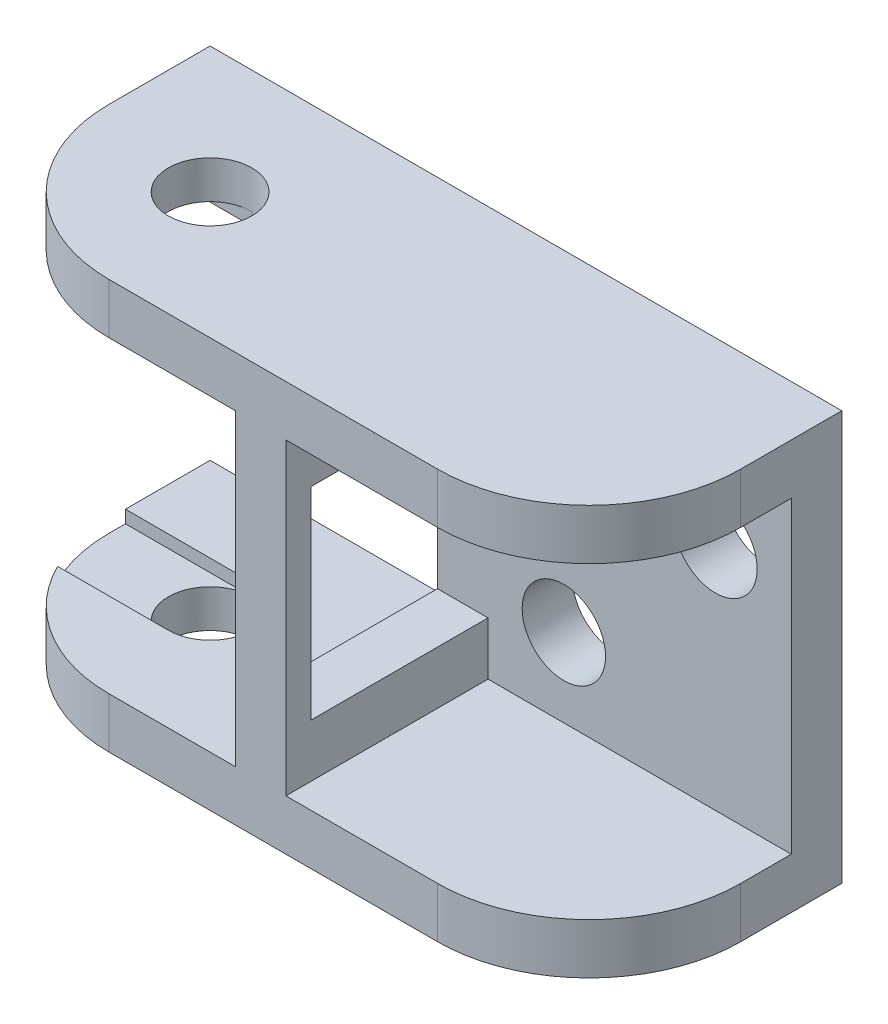
SolidWorks part; units mm, degrees
material "Сталь 45 ГОСТ 1050-2013"
ref_plane "Спереди" through (0, 0, 0) normal (0, 0, 1) x (1, 0, 0)
ref_plane "Сверху" through (0, 0, 0) normal (0, 1, 0) x (1, 0, 0)
ref_plane "Справа" through (0, 0, 0) normal (1, 0, 0) x (0, 0, -1)
sketch "Эскиз2" plane through (0, 0, 0) normal (0, 0, 1) x (1, 0, 0)
  line L0 (0, 0) -> (0, 2)
  line L1 (0, 2) -> (13, 2)
  line L2 (13, 2) -> (13, -0.1)
  line L3 (13, -0.1) -> (24, -0.1)
  line L4 (24, -0.1) -> (24, -2.1)
  line L5 (24, -2.1) -> (11, -2.1)
  line L6 (11, -2.1) -> (11, 0)
  line L7 (11, 0) -> (0, 0)
  dimension "D1" = 2
  dimension "D2" = 24
  dimension "D3" = 2
  dimension "D4" = 11
  dimension "D5" = 0.1
  dimension "D6" = 2
extrude "Бобышка-Вытянуть2" add sketch "Эскиз2" along normal blind 10
sketch "Эскиз3" plane through (0, -0.1, 0) normal (0, 1, 0) x (1, 0, 0)
  line L0 (0, -10) -> (0, 0) construction
  line L1 (24, -10) -> (24, 0) construction
  circle A0 centre (6, -5) radius 1.5 construction
  circle A1 centre (18.1, -5) radius 1.5
  point P5 (0, -5)
  dimension "D1" = 3
  dimension "D2" = 5.9
  dimension "D3" = 6
extrude "Бобышка-Вытянуть3" add sketch "Эскиз3" along normal blind 1.5
sketch "Эскиз5" plane through (0, 0, 0) normal (0, -1, 0) x (1, 0, 0)
  line L0 (0, 10) -> (0, 0) construction
  circle A0 centre (5, 5) radius 1.65
  point P2 (0, 5)
  dimension "D1" = 3.3
  dimension "D2" = 5
extrude "Вырез-Вытянуть2" cut sketch "Эскиз5" against normal through all
fillet "Скругление1" radius 6 2 edges at (24, -1.1, 10) (0, 1, 10)
sketch "Эскиз6" plane through (0, -2.1, 0) normal (0, -1, 0) x (-1, 0, 0)
  line L1 (-11, 0) -> (-21, 0)
  line L2 (-11, 0) -> (-11, -1)
  line L3 (-11, -1) -> (-21, -1)
  line L4 (-21, 0) -> (-21, -1)
  line L5 (-11, 0) -> (-21, -1) construction
  line L6 (-11, -1) -> (-21, 0) construction
  line L7 (-11, -9) -> (-16, -9)
  line L8 (-11, -9) -> (-11, -10)
  line L9 (-11, -10) -> (-16, -10)
  line L10 (-16, -9) -> (-16, -10)
  line L11 (-11, -9) -> (-16, -10) construction
  line L12 (-11, -10) -> (-16, -9) construction
  point P0 (-16, -0.5)
  point P5 (-13.5, -9.5)
  dimension "D1" = 1
  dimension "D2" = 10
  dimension "D3" = 5
extrude "Бобышка-Вытянуть4" add sketch "Эскиз6" along normal blind 4
sketch "Эскиз7" plane through (0, 0, 0) normal (0, -1, 0) x (1, 0, 0)
  line L1 (-0.6896, 3.35) -> (5, 3.35)
  line L2 (-0.6896, 3.35) -> (-0.6896, 6.65)
  line L3 (-0.6896, 6.65) -> (5, 6.65)
  line L4 (5, 3.35) -> (5, 6.65)
  line L5 (-0.6896, 3.35) -> (5, 6.65) construction
  line L6 (-0.6896, 6.65) -> (5, 3.35) construction
  circle A0 centre (5, 5) radius 1.65 construction
  point P0 (2.1552, 5)
extrude "Вырез-Вытянуть3" cut sketch "Эскиз7" against normal blind 0.5
mirror "Зеркальное отражение1" about plane through (0, -6.1, 0) normal (0, 1, 0) of bodies 111 109
sketch "Эскиз8" plane through (0, 0, 10) normal (0, 0, 1) x (1, 0, 0)
  line L0 (13, -14.2) -> (6, -14.2) construction
  line L1 (27.1965, -14.2) -> (13, -14.2)
  line L2 (27.1965, -14.2) -> (27.1965, 2)
  line L3 (27.1965, 2) -> (13, 2)
  line L4 (13, -14.2) -> (13, 2)
  line L5 (27.1965, -14.2) -> (13, 2) construction
  line L6 (27.1965, 2) -> (13, -14.2) construction
  point P0 (20.0983, -6.1)
  point P6 (13, -14.2)
extrude "Вырез-Вытянуть4" cut sketch "Эскиз8" against normal through all
other "Переместить грань1" face at (13, -6.1, 5) parameters "D1"=12
sketch "Эскиз9" plane through (0, 0, 10) normal (0, 0, 1) x (1, 0, 0)
  line L0 (6, 0) -> (11, 0) construction
  line L1 (29.7709, -12.2) -> (13, -12.2)
  line L2 (29.7709, -12.2) -> (29.7709, 0)
  line L3 (29.7709, 0) -> (13, 0)
  line L4 (13, -12.2) -> (13, 0)
  line L5 (29.7709, -12.2) -> (13, 0) construction
  line L6 (29.7709, 0) -> (13, -12.2) construction
  line L7 (6, -12.2) -> (11, -12.2) construction
  line L8 (11, 0) -> (11, -12.2) construction
  point P0 (21.3855, -6.1)
  point P7 (0, 0)
  dimension "D1" = 2
extrude "Вырез-Вытянуть5" cut sketch "Эскиз9" against normal up to surface (9 mm away) up to face at (18, -6.1, 1)
sketch "Эскиз10" plane through (0, 0, 1) normal (0, 0, 1) x (1, 0, 0)
  line L0 (27, -6.1) -> (-49973, -6.1) construction
  line L1 (25, -12.2) -> (25, 0) construction
  line L2 (19, 0) -> (19, -50000) construction
  line L3 (25, 0) -> (13, 0) construction
  circle A0 centre (16, -9.1) radius 1.65
  circle A1 centre (22, -3.1) radius 1.65
  point P8 (25, -6.1)
  point P13 (19, 0)
  dimension "D1" = 3.3
  dimension "D2" = 3
  dimension "D3" = 3
  dimension "D4" = 3
  dimension "D5" = 3
extrude "Вырез-Вытянуть6" cut sketch "Эскиз10" against normal through all
fillet "Скругление2" radius 6 2 edges at (25, -13.2, 10) (25, 1, 10)
other "Переместить грань2" face at (17.65, -9.1, 1) parameters "D1"=1
